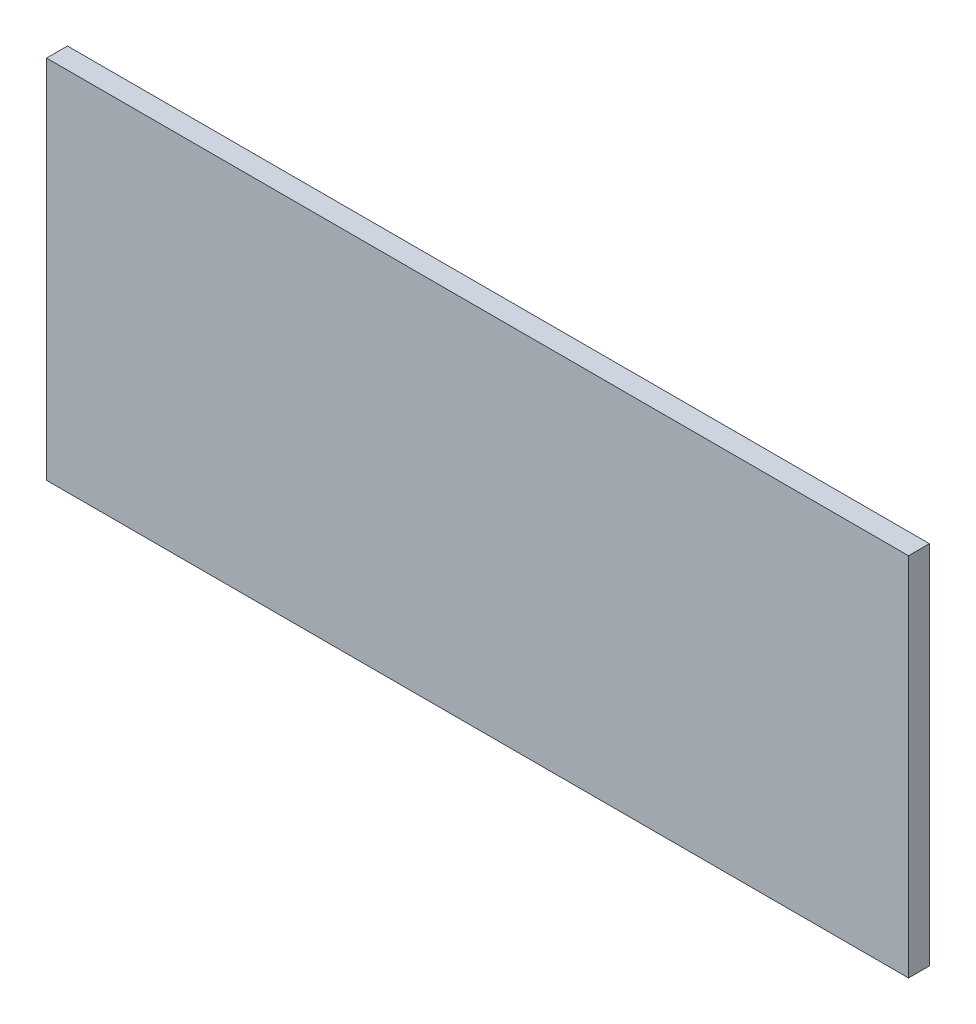
SolidWorks part; units mm, degrees
material "Maple"
ref_plane "Front Plane" through (0, 0, 0) normal (0, 0, 1) x (1, 0, 0)
ref_plane "Top Plane" through (0, 0, 0) normal (0, 1, 0) x (1, 0, 0)
ref_plane "Right Plane" through (0, 0, 0) normal (1, 0, 0) x (0, 0, -1)
sketch "Sketch1" plane through (0, 0, 0) normal (0, 0, 1) x (1, 0, 0)
  line L1 (82.5, -35) -> (-82.5, -35)
  line L2 (82.5, -35) -> (82.5, 35)
  line L3 (82.5, 35) -> (-82.5, 35)
  line L4 (-82.5, -35) -> (-82.5, 35)
  line L5 (82.5, -35) -> (-82.5, 35) construction
  line L6 (82.5, 35) -> (-82.5, -35) construction
  point P0 (0, 0)
  dimension "D1" = 70
  dimension "D2" = 165
extrude "Boss-Extrude1" add sketch "Sketch1" along normal blind 4
